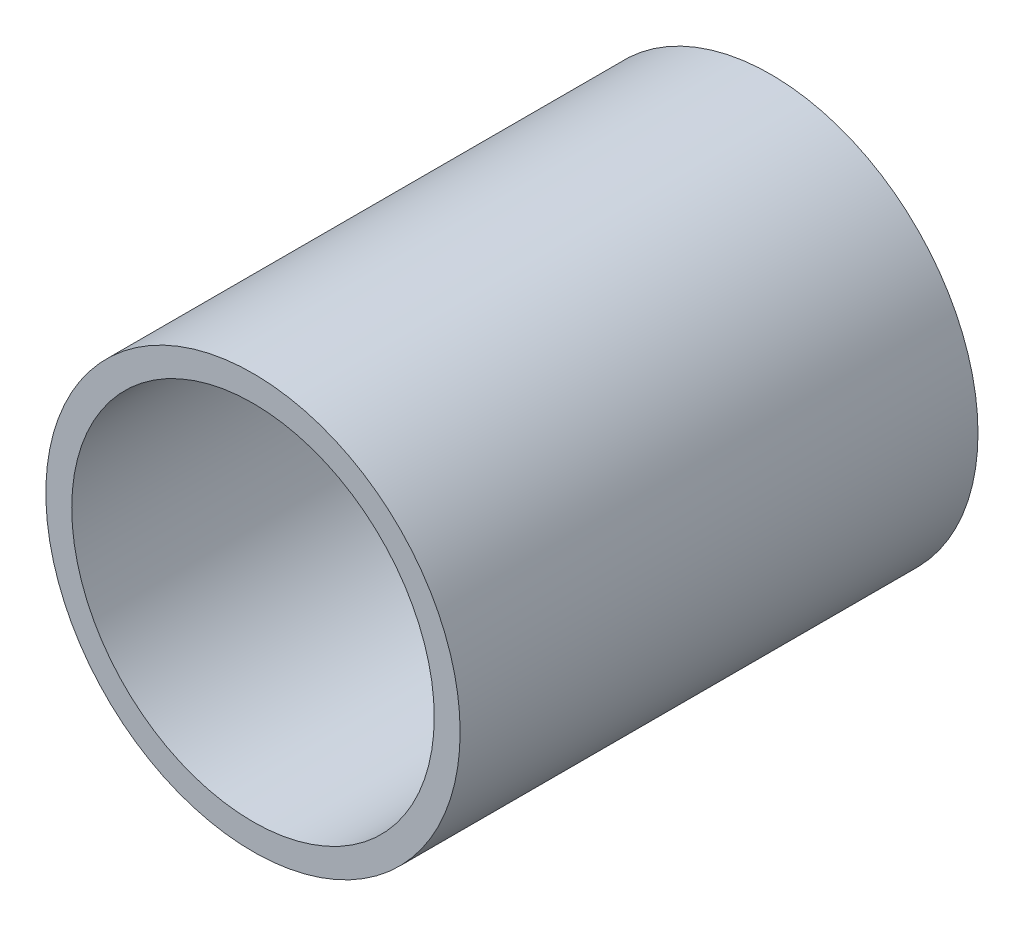
SolidWorks part; units mm, degrees
ref_plane "Plan1" through (0, 0, 0) normal (0, 0, 1) x (1, 0, 0)
ref_plane "Plan2" through (0, 0, 0) normal (0, 1, 0) x (1, 0, 0)
ref_plane "Plan3" through (0, 0, 0) normal (1, 0, 0) x (0, 0, -1)
sketch "Esquisse1" plane through (0, 0, 0) normal (0, 0, 1) x (1, 0, 0)
  circle A0 centre (0, 0) radius 3.5
  circle A1 centre (0, 0) radius 4
  dimension "D1" = 7
  dimension "D2" = 8
extrude "Base-Extrusion" add sketch "Esquisse1" along normal blind 10
